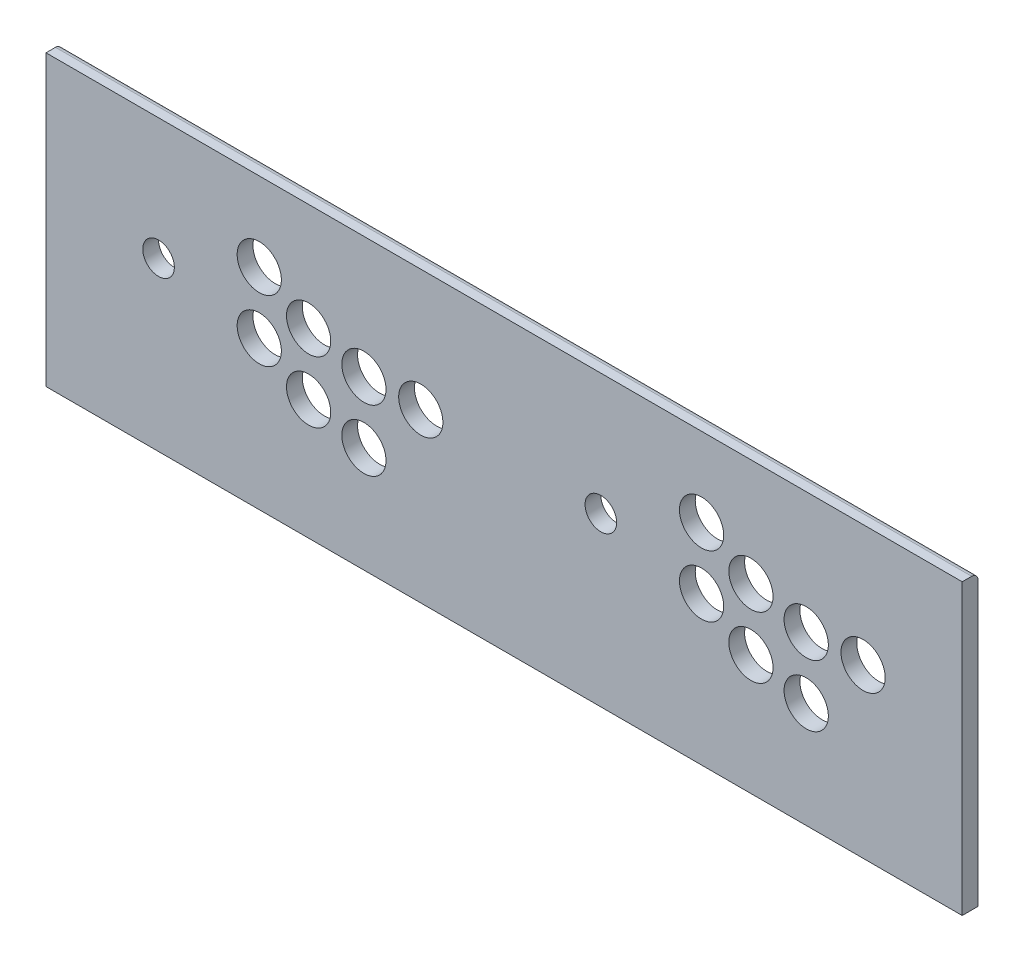
SolidWorks part; units mm, degrees
ref_plane "Plan de face" through (0, 0, 0) normal (0, 0, 1) x (1, 0, 0)
ref_plane "Plan de dessus" through (0, 0, 0) normal (0, 1, 0) x (1, 0, 0)
ref_plane "Plan de droite" through (0, 0, 0) normal (1, 0, 0) x (0, 0, -1)
sketch "Esquisse1" plane through (0, 0, 0) normal (0, 0, 1) x (1, 0, 0)
  line L1 (0, 0) -> (580, 0)
  line L2 (0, 0) -> (0, 183)
  line L3 (0, 183) -> (580, 183)
  line L4 (580, 0) -> (580, 183)
  dimension "D1" = 183
  dimension "D2" = 580
extrude "Boss.-Extru.1" add sketch "Esquisse1" along normal blind 10
sketch "Esquisse3" plane through (0, 0, 0) normal (0, 0, -1) x (-1, 0, 0)
  line L13 (-290, 183) -> (-290, 0) construction
  line L14 (-580, 183) -> (0, 183) construction
  line L15 (0, 0) -> (-580, 0) construction
  circle A2 centre (-201.25, 67) radius 14
  circle A3 centre (-71.25, 106) radius 10
  circle A4 centre (-166.25, 76) radius 14
  circle A5 centre (-135, 94) radius 14
  circle A6 centre (-237.25, 106) radius 14
  circle A7 centre (-201.25, 106) radius 14
  circle A8 centre (-166.25, 115) radius 14
  circle A9 centre (-135, 133) radius 14
  dimension "D13" = 20
  dimension "D2" = 28
extrude "Enlèv. mat.-Extru.1" cut sketch "Esquisse3" against normal blind 10
pattern_linear "Répétition linéaire1" count 2 spacing 280 along (1, 0, 0) of "Enlèv. mat.-Extru.1"
fillet "Congé1" radius 4 1 edges at (290, 183, 0)
